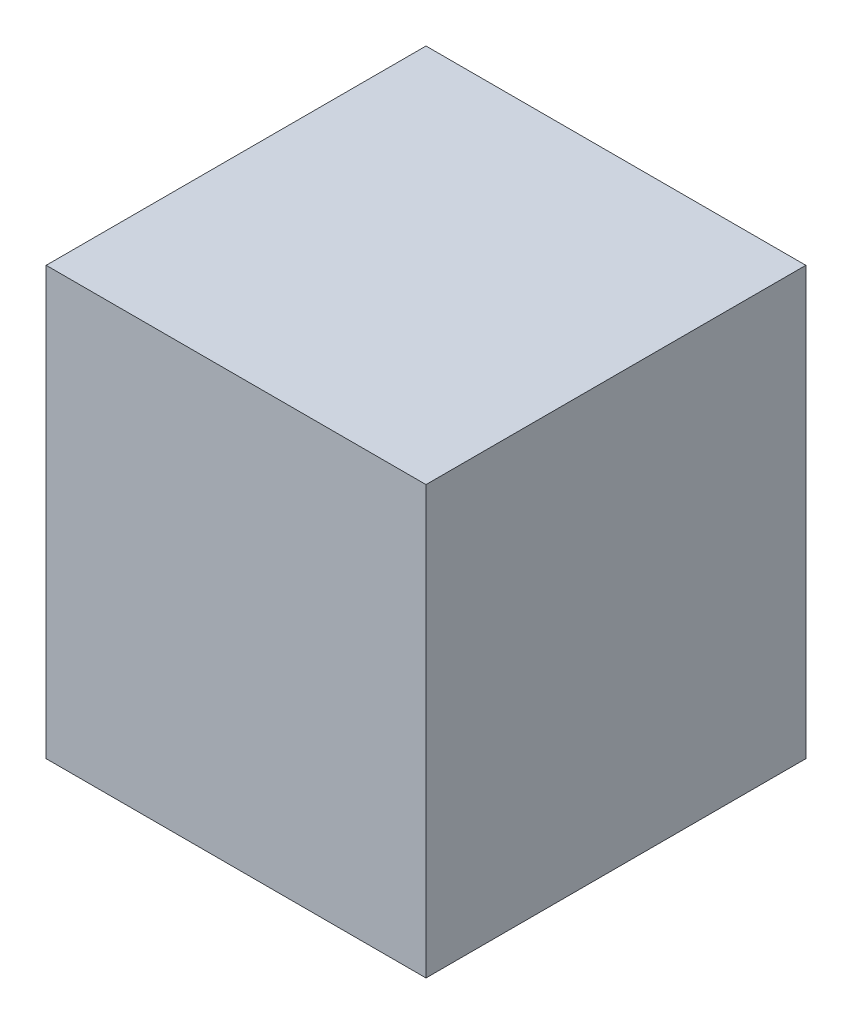
SolidWorks part; units mm, degrees
ref_plane "Front Plane" through (0, 0, 0) normal (0, 0, 1) x (1, 0, 0)
ref_plane "Top Plane" through (0, 0, 0) normal (0, 1, 0) x (1, 0, 0)
ref_plane "Right Plane" through (0, 0, 0) normal (1, 0, 0) x (0, 0, -1)
sketch "Sketch1" plane through (0, 0, 0) normal (0, 1, 0) x (1, 0, 0)
  line L0 (-50.8, -50.8) -> (50.8, 50.8) construction
  line L1 (-50.8, 50.8) -> (50.8, 50.8)
  line L2 (-50.8, 50.8) -> (-50.8, -50.8)
  line L3 (-50.8, -50.8) -> (50.8, -50.8)
  line L4 (50.8, 50.8) -> (50.8, -50.8)
  dimension "D1" = 101.6
  dimension "D2" = 101.6
extrude "Boss-Extrude1" add sketch "Sketch1" along normal blind 114.3
